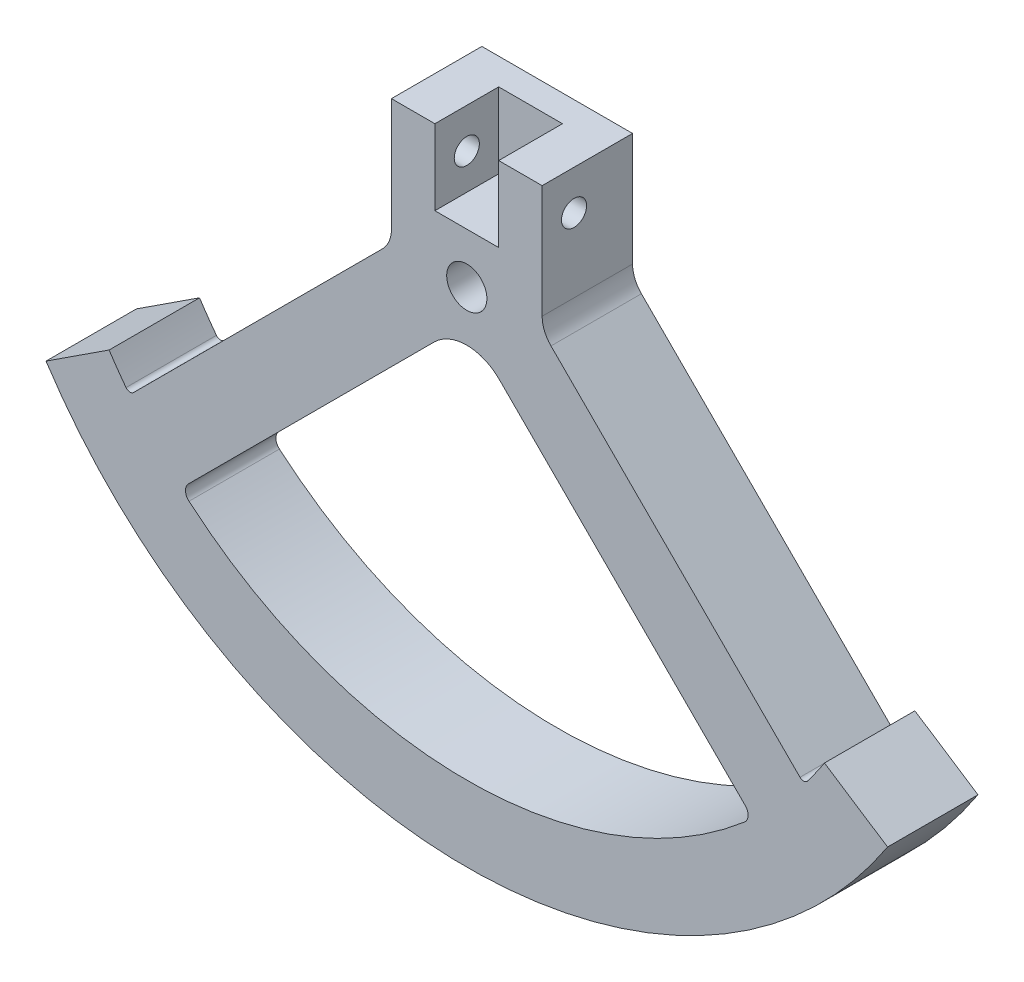
SolidWorks part; units mm, degrees
ref_plane "Plan de face" through (0, 0, 0) normal (0, 0, 1) x (1, 0, 0)
ref_plane "Plan de dessus" through (0, 0, 0) normal (0, 1, 0) x (1, 0, 0)
ref_plane "Plan de droite" through (0, 0, 0) normal (1, 0, 0) x (0, 0, -1)
sketch "Esquisse1" plane through (0, 0, 0) normal (0, 0, 1) x (1, 0, 0)
  line L0 (0, 63.7812) -> (0, -69.4456) construction
  line L1 (15, 25) -> (-15, 25)
  line L2 (-15, 25) -> (-15, 0)
  line L3 (-83.7605, -54.6276) -> (-71.1964, -46.4335)
  line L4 (-55.4089, -61.6221) -> (-6.4645, -12.6777)
  line L5 (55.4089, -61.6221) -> (6.4645, -12.6777)
  line L6 (-83.7605, -54.6276) -> (0, 0) construction
  line L7 (15, 25) -> (15, 0)
  line L8 (-15, 0) -> (-67.1343, -52.1343)
  line L9 (15, 0) -> (67.1343, -52.1343)
  line L10 (83.7605, -54.6276) -> (71.1964, -46.4335)
  arc A0 (-83.7605, -54.6276) -> (83.7605, -54.6276) centre (0, 0) ccw
  circle A1 centre (0, 0) radius 4
  arc A2 (55.2957, -64.5552) -> (-55.2957, -64.5552) centre (0, 0) cw
  arc A3 (-6.4645, -12.6777) -> (6.4645, -12.6777) centre (0, -19.1421) cw
  arc A4 (-55.2957, -64.5552) -> (-55.4089, -61.6221) centre (-53.9947, -63.0363) cw
  arc A5 (55.2957, -64.5552) -> (55.4089, -61.6221) centre (53.9947, -63.0363) ccw
  circle A6 centre (0, 0) radius 85 construction
  arc A7 (-71.1964, -46.4335) -> (-67.1343, -52.1343) centre (0, 0) ccw
  arc A8 (71.1964, -46.4335) -> (67.1343, -52.1343) centre (0, 0) cw
  point P2 (0, -10)
  point P15 (0, 25)
  point P22 (0, -4)
  dimension "D1" = 2
  dimension "D3" = 100
  dimension "D4" = 30
  dimension "D7" = 15
  dimension "D9" = 8
  dimension "D10" = 6
  dimension "D2" = 15
  dimension "D5" = 25
  dimension "D6" = 90
  dimension "D8" = 25
  dimension "D11" = 7
extrude "Boss.-Extru.1" add sketch "Esquisse1" along normal blind 18
sketch "Esquisse2" plane through (0, 25, 0) normal (0, 1, 0) x (1, 0, 0)
  line L0 (15, -18) -> (-15, -18) construction
  line L1 (6.35, -5.3) -> (-6.35, -5.3)
  line L2 (6.35, -5.3) -> (6.35, -18)
  line L3 (6.35, -18) -> (-6.35, -18)
  line L4 (-6.35, -5.3) -> (-6.35, -18)
  line L5 (6.35, -5.3) -> (-6.35, -18) construction
  line L6 (6.35, -18) -> (-6.35, -5.3) construction
  point P0 (0, -11.65)
  dimension "D1" = 12.7
  dimension "D2" = 12.7
extrude "Enlèv. mat.-Extru.1" cut sketch "Esquisse2" against normal blind 15
sketch "Esquisse3" plane through (-15, 0, 0) normal (-1, 0, 0) x (0, 0, 1)
  line L0 (5.3, 35.8353) -> (5.3, 6.2502) construction
  line L1 (5.3, 10) -> (5.3, 25) construction
  line L2 (18, 10) -> (5.3, 10) construction
  line L3 (5.3, 10) -> (18, 10) construction
  line L4 (11.65, 10) -> (11.65, 25) construction
  line L5 (18, 25) -> (0, 25) construction
  circle A0 centre (11.65, 17.125) radius 2.5
  point P8 (11.65, 17.125)
  dimension "D1" = 5
  dimension "D2" = 7.125
extrude "Enlèv. mat.-Extru.2" cut sketch "Esquisse3" against normal up to surface (30 mm away) up to face at (15, 12.5, 9)
sketch "Esquisse4" plane through (0, 0, 18) normal (0, 0, 1) x (1, 0, 0)
  line L0 (40.9268, -38.656) -> (82.4185, -80.1478)
  line L1 (82.4185, -80.1478) -> (84.5412, -78.0251)
  line L2 (84.5412, -78.0251) -> (43.0494, -36.5334)
  line L4 (4.6428, -0.2494) -> (76.9994, -72.606) construction
  line L6 (67.1343, -52.1343) -> (15, 0) construction
  line L7 (55.4089, -61.6221) -> (6.4645, -12.6777) construction
  arc A0 (40.9268, -38.656) -> (43.0494, -36.5334) centre (41.0534, -36.66) cw
  arc A1 (-83.7605, -54.6276) -> (83.7605, -54.6276) centre (0, 0) ccw construction
  point P11 (72.8732, -68.4798)
  dimension "D2" = 3.0018
  dimension "D1" = 2
  dimension "D3" = 45
  dimension "D4" = 15
fillet "Congé1" radius 1 2 edges at (67.1343, -52.1343, 9) (-67.1343, -52.1343, 9)
fillet "Congé2" radius 6 2 edges at (-15, 0, 9) (15, 0, 9)
